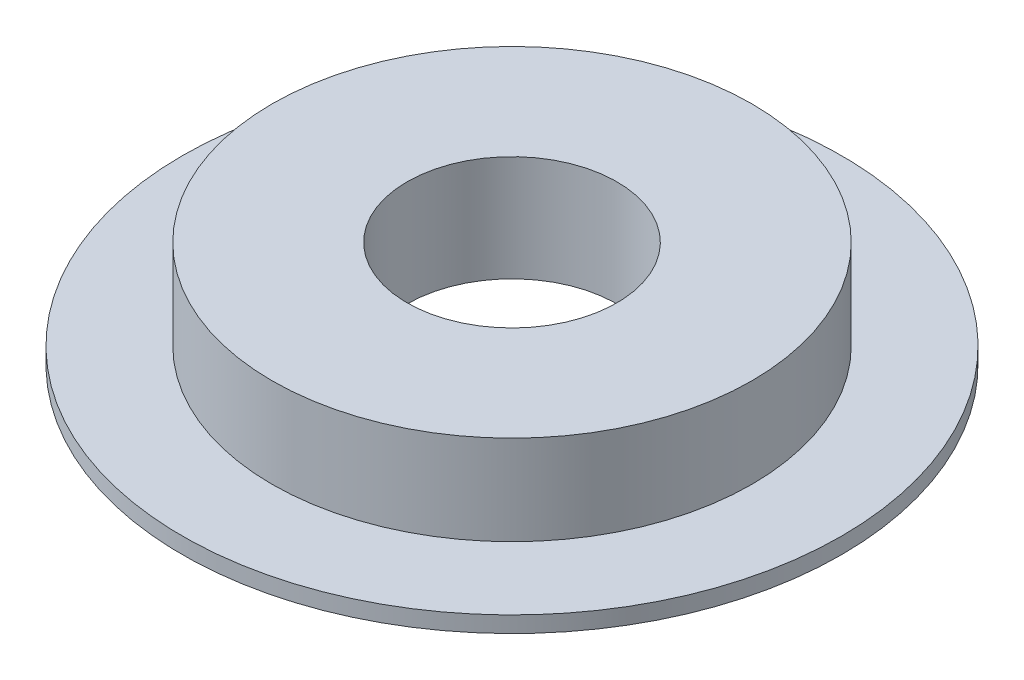
SolidWorks part; units mm, degrees
ref_plane "Alzado" through (0, 0, 0) normal (0, 0, 1) x (1, 0, 0)
ref_plane "Planta" through (0, 0, 0) normal (0, 1, 0) x (1, 0, 0)
ref_plane "Vista lateral" through (0, 0, 0) normal (1, 0, 0) x (0, 0, -1)
sketch "Croquis1" plane through (0, 0, 0) normal (0, 0, 1) x (1, 0, 0)
  line L0 (-29.2716, 13.9729) -> (-29.2716, -36.0271) construction
  line L1 (-29.2716, -11.0271) -> (-40.7716, -11.0271) construction
  line L2 (-40.9716, 8.9729) -> (-40.9716, -2.8271)
  line L3 (-29.2716, 8.9729) -> (-56.0216, 8.9729) construction
  line L4 (-40.9716, 8.9729) -> (-56.0216, 8.9729)
  line L5 (-56.0216, 8.9729) -> (-56.0216, -1.0271)
  line L6 (-56.0216, -1.0271) -> (-66.0216, -1.0271)
  line L7 (-66.0216, -1.0271) -> (-66.0216, -2.8271)
  line L8 (-66.0216, -2.8271) -> (-40.9716, -2.8271)
  dimension "D1" = 26.75
  dimension "D2" = 11.5
  dimension "D3" = 1.8
  dimension "D4" = 10
  dimension "D5" = 11.7
  dimension "D6" = 10
revolve "Revolución1" add sketch "Croquis1" angle 360 about L0
